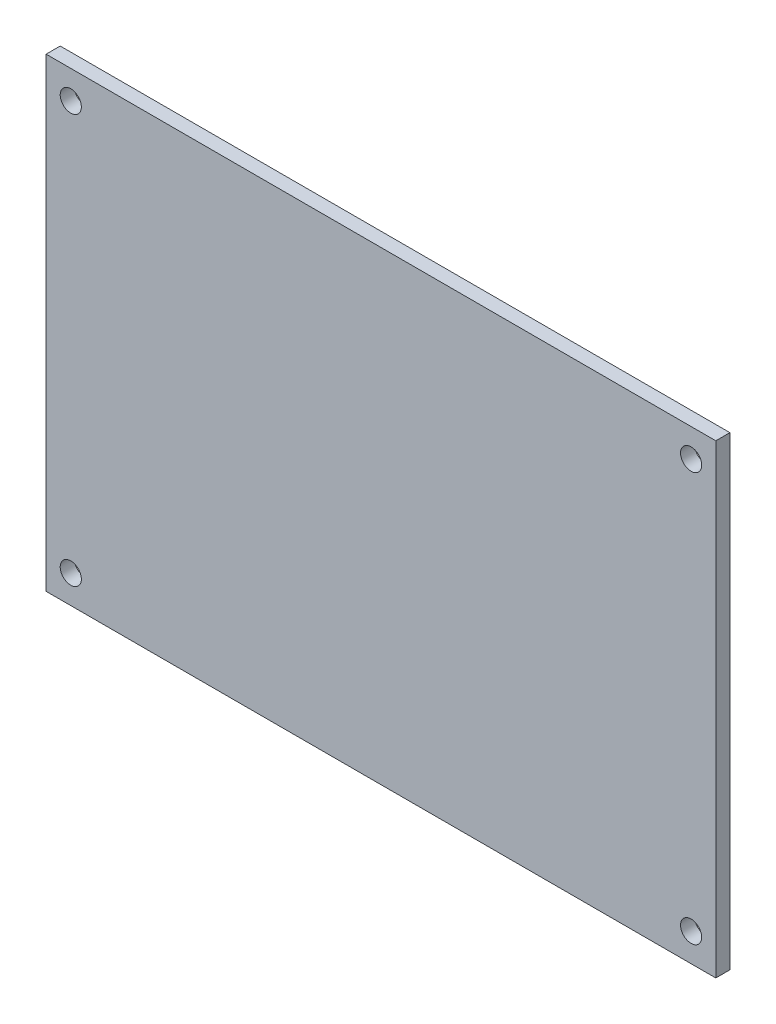
SolidWorks part; units mm, degrees
ref_plane "Front Plane" through (0, 0, 0) normal (0, 0, 1) x (1, 0, 0)
ref_plane "Top Plane" through (0, 0, 0) normal (0, 1, 0) x (1, 0, 0)
ref_plane "Right Plane" through (0, 0, 0) normal (1, 0, 0) x (0, 0, -1)
sketch "Sketch1" plane through (0, 0, 0) normal (0, 0, 1) x (1, 0, 0)
  line L1 (-95, 66) -> (0, 66)
  line L2 (-95, 66) -> (-95, 0)
  line L3 (-95, 0) -> (0, 0)
  line L4 (0, 66) -> (0, 0)
  dimension "D1" = 95
  dimension "D2" = 66
extrude "Boss-Extrude1" add sketch "Sketch1" along normal blind 2
sketch "Sketch2" plane through (0, 0, 2) normal (0, 0, 1) x (1, 0, 0)
  line L0 (0, 66) -> (-95, 66) construction
  line L1 (-3.5, 4) -> (-91.5, 4) construction
  line L2 (-3.5, 4) -> (-3.5, 62) construction
  line L3 (-3.5, 62) -> (-91.5, 62) construction
  line L4 (-91.5, 4) -> (-91.5, 62) construction
  line L5 (-3.5, 4) -> (-91.5, 62) construction
  line L6 (-3.5, 62) -> (-91.5, 4) construction
  line L7 (-95, 66) -> (-95, 0) construction
  circle A1 centre (-91.5, 62) radius 1.5
  circle A2 centre (-3.5, 62) radius 1.5
  circle A3 centre (-3.5, 4) radius 1.5
  circle A4 centre (-91.5, 4) radius 1.5
  point P0 (-47.5, 33)
  point P7 (-47.5, 66)
  point P10 (-95, 33)
  dimension "D1" = 3
  dimension "D2" = 88
  dimension "D3" = 58
extrude "Cut-Extrude1" cut sketch "Sketch2" against normal blind 2
